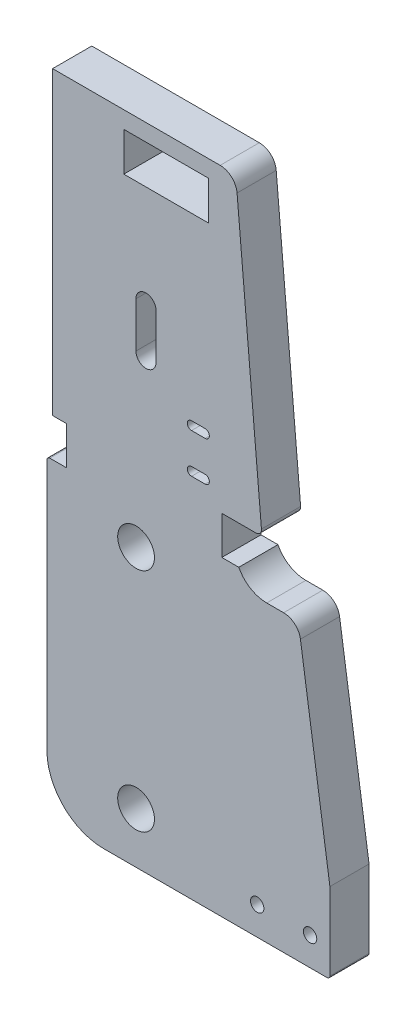
SolidWorks part; units mm, degrees
ref_plane "Front Plane" through (0, 0, 0) normal (0, 0, 1) x (1, 0, 0)
ref_plane "Top Plane" through (0, 0, 0) normal (0, 1, 0) x (1, 0, 0)
ref_plane "Right Plane" through (0, 0, 0) normal (1, 0, 0) x (0, 0, -1)
sketch "Sketch1" plane through (0, 0, 0) normal (0, 0, 1) x (1, 0, 0)
  line L0 (72.3999, 63.25) -> (69.9999, 63.25)
  line L1 (69.9999, 64.75) -> (72.3999, 64.75)
  line L2 (72.3999, 70.25) -> (69.9999, 70.25)
  line L3 (69.9999, 71.75) -> (72.3999, 71.75)
  line L4 (60.1749, 77.5) -> (60.1749, 85.5)
  line L5 (63.7249, 85.5) -> (63.7249, 77.5)
  line L6 (54.4499, -1.5) -> (93.9499, -1.5)
  line L7 (94.4499, -1) -> (94.4499, 12.6867)
  line L8 (94.4499, 12.6867) -> (89.2434, 47.9383)
  line L9 (86.2756, 50.5) -> (83.2802, 50.5)
  line L10 (78.3499, 53.5) -> (75.3499, 53.5)
  line L11 (75.3499, 53.5) -> (75.3499, 60.26)
  line L12 (75.3499, 60.26) -> (81.3586, 60.26)
  line L13 (82.3548, 61.3472) -> (78.044, 110.6195)
  line L14 (75.0554, 113.358) -> (45.4499, 113.358)
  line L15 (45.4499, 113.358) -> (45.4499, 60.26)
  line L16 (45.4499, 60.26) -> (47.9499, 60.26)
  line L17 (47.9499, 60.26) -> (47.9499, 53.5)
  line L18 (47.9499, 53.5) -> (44.9499, 53.5)
  line L19 (44.4499, 53) -> (44.4499, 8.5)
  line L20 (58.0339, 110.358) -> (58.0339, 103.5)
  line L21 (58.0339, 103.5) -> (73.0339, 103.5)
  line L22 (73.0339, 103.5) -> (73.0339, 110.358)
  line L23 (73.0339, 110.358) -> (58.0339, 110.358)
  circle A0 centre (60.1999, 47.5) radius 3.25
  circle A1 centre (60.1999, 7.5) radius 3.25
  circle A2 centre (81.6027, 3.5) radius 1.1811
  circle A3 centre (90.9499, 3.5) radius 1.1811
  arc A4 (69.9999, 64.75) -> (69.9999, 63.25) centre (69.9999, 64) ccw
  arc A5 (72.3999, 63.25) -> (72.3999, 64.75) centre (72.3999, 64) ccw
  arc A6 (69.9999, 71.75) -> (69.9999, 70.25) centre (69.9999, 71) ccw
  arc A7 (72.3999, 70.25) -> (72.3999, 71.75) centre (72.3999, 71) ccw
  arc A8 (63.7249, 85.5) -> (60.1749, 85.5) centre (61.9499, 85.5) ccw
  arc A9 (60.1749, 77.5) -> (63.7249, 77.5) centre (61.9499, 77.5) ccw
  arc A10 (44.4499, 8.5) -> (54.4499, -1.5) centre (54.4499, 8.5) ccw
  arc A11 (93.9499, -1.5) -> (94.4499, -1) centre (93.9499, -1) ccw
  arc A12 (89.2434, 47.9383) -> (86.2756, 50.5) centre (86.2756, 47.5) ccw
  arc A13 (78.3499, 53.5) -> (83.2802, 50.5) centre (83.2802, 56.0512) ccw
  arc A14 (81.3586, 60.26) -> (82.3548, 61.3472) centre (81.3586, 61.26) ccw
  arc A15 (78.044, 110.6195) -> (75.0554, 113.358) centre (75.0554, 110.358) ccw
  arc A16 (44.9499, 53.5) -> (44.4499, 53) centre (44.9499, 53) ccw
extrude "Boss-Extrude1" add sketch "Sketch1" along normal blind 6.92
